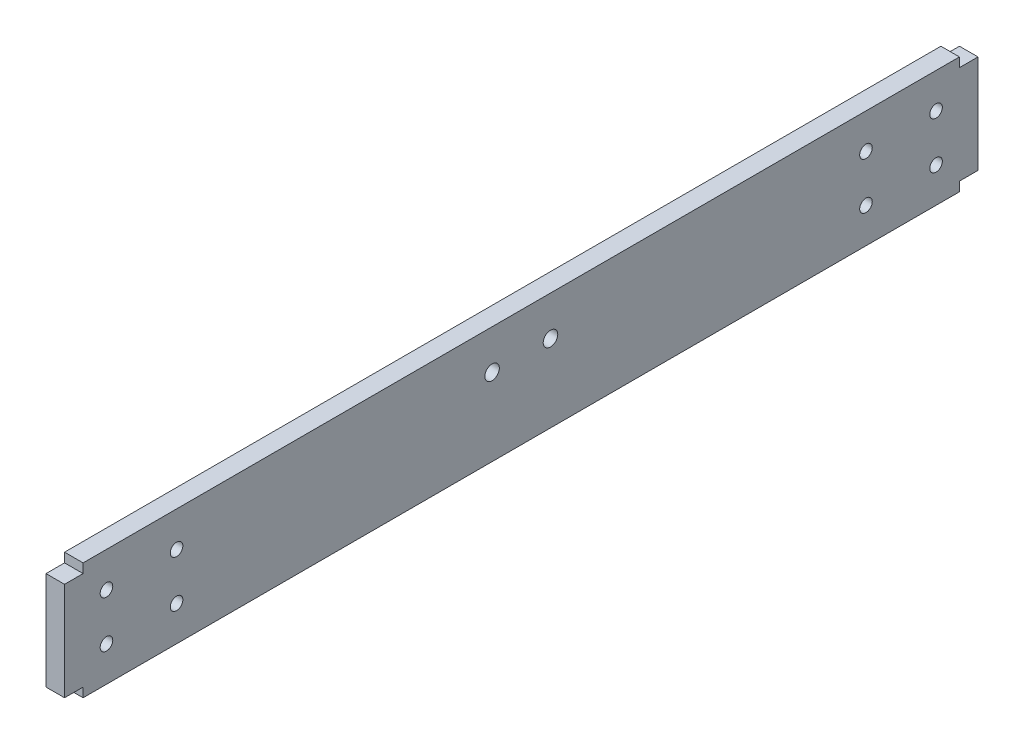
SolidWorks part; units mm, degrees
ref_plane "Front Plane" through (0, 0, 0) normal (0, 0, 1) x (1, 0, 0)
ref_plane "Top Plane" through (0, 0, 0) normal (0, 1, 0) x (1, 0, 0)
ref_plane "Right Plane" through (0, 0, 0) normal (1, 0, 0) x (0, 0, -1)
sketch "Sketch1" plane through (0, 0, 0) normal (1, 0, 0) x (0, 0, -1)
  line L0 (-150, -20) -> (-150, 20)
  line L1 (-150, -20) -> (150, -20)
  line L2 (-150, 20) -> (150, 20)
  line L3 (150, -20) -> (150, 20)
  line L4 (-150, -20) -> (150, 20) construction
  line L5 (-150, 20) -> (150, -20) construction
  point P1 (0, 0)
  dimension "D1" = 300
  dimension "D2" = 40
extrude "Boss-Extrude1" add sketch "Sketch1" along normal blind 6.35
sketch "Sketch2" plane through (6.35, 0, 0) normal (1, 0, 0) x (0, 0, -1)
  line L0 (-156.35, 16.825) -> (-150, 16.825)
  line L1 (-156.35, 16.825) -> (-156.35, -16.825)
  line L2 (-150, 16.825) -> (-150, -16.825)
  line L3 (-156.35, -16.825) -> (-150, -16.825)
  line L4 (-156.35, 16.825) -> (-150, -16.825) construction
  line L5 (-150, 16.825) -> (-156.35, -16.825) construction
  line L6 (156.35, 16.825) -> (150, 16.825)
  line L7 (156.35, 16.825) -> (156.35, -16.825)
  line L8 (150, 16.825) -> (150, -16.825)
  line L9 (156.35, -16.825) -> (150, -16.825)
  line L10 (156.35, 16.825) -> (150, -16.825) construction
  line L11 (150, 16.825) -> (156.35, -16.825) construction
  line L12 (-150, 20) -> (-150, -20) construction
  line L13 (150, -20) -> (150, 20) construction
  point P1 (-153.175, 0)
  point P2 (153.175, 0)
  dimension "D1" = 33.65
  dimension "D2" = 6.35
extrude "Boss-Extrude2" add sketch "Sketch2" against normal blind 6.35
sketch "Sketch3" plane through (6.35, 0, 0) normal (1, 0, 0) x (0, 0, -1)
  line L0 (10, 6.5) -> (-10, 6.5) construction
  point P3 (0, 6.5)
  dimension "D1" = 20
  dimension "D2" = 6.5
hole_wizard "#10 Clearance Hole1" positions "Sketch5" profile "Sketch4" hole size "#10" standard "ANSI Inch" end condition through all
sketch "Sketch5" plane through (6.35, 0, 0) normal (1, 0, 0) x (0, 0, -1)
  point P0 (-10, 6.5)
  point P3 (10, 6.5)
sketch "Sketch4" plane through (6.35, 6.5, 10) normal (0, 1, 0) x (0, 0, -1)
  line L0 (0, 0) -> (0, 6.35)
  line L1 (0, 6.35) -> (2.4892, 6.35)
  line L2 (2.4892, 6.35) -> (2.4892, 0)
  line L5 (2.4892, 0) -> (0, 0)
  line L11 (0, -6.35) -> (0, 107.95) construction
  dimension "Thru Hole Dia." = 4.9784
  dimension "Thru Hole Depth" = 6.35
sketch "Sketch6" plane through (6.35, 0, 0) normal (1, 0, 0) x (0, 0, -1)
  line L0 (-142, -8) -> (-118, -8) construction
  line L1 (-142, -8) -> (-142, 8) construction
  line L2 (-118, -8) -> (-118, 8) construction
  line L3 (-142, 8) -> (-118, 8) construction
  line L4 (-142, -8) -> (-118, 8) construction
  line L5 (-118, -8) -> (-142, 8) construction
  line L6 (142, -8) -> (142, 8) construction
  line L7 (142, -8) -> (118, -8) construction
  line L8 (142, 8) -> (118, 8) construction
  line L9 (118, -8) -> (118, 8) construction
  line L10 (142, -8) -> (118, 8) construction
  line L11 (142, 8) -> (118, -8) construction
  point P1 (-130, 0)
  point P2 (130, 0)
  dimension "D1" = 24
  dimension "D2" = 16
  dimension "D3" = 130
  dimension "D4" = 130
hole_wizard "#8 Clearance Hole1" positions "Sketch8" profile "Sketch7" hole size "#8" standard "ANSI Inch" end condition through all
sketch "Sketch8" plane through (6.35, 0, 0) normal (1, 0, 0) x (0, 0, -1)
  point P0 (-142, 8)
  point P3 (-118, 8)
  point P6 (-118, -8)
  point P9 (-142, -8)
  point P12 (118, 8)
  point P15 (142, 8)
  point P18 (142, -8)
  point P21 (118, -8)
sketch "Sketch7" plane through (6.35, 8, 142) normal (0, 1, 0) x (0, 0, -1)
  line L0 (0, 0) -> (0, 6.35)
  line L1 (0, 6.35) -> (2.1526, 6.35)
  line L2 (2.1526, 6.35) -> (2.1526, 0)
  line L5 (2.1526, 0) -> (0, 0)
  line L11 (0, -6.35) -> (0, 107.95) construction
  dimension "Thru Hole Dia." = 4.3053
  dimension "Thru Hole Depth" = 6.35
